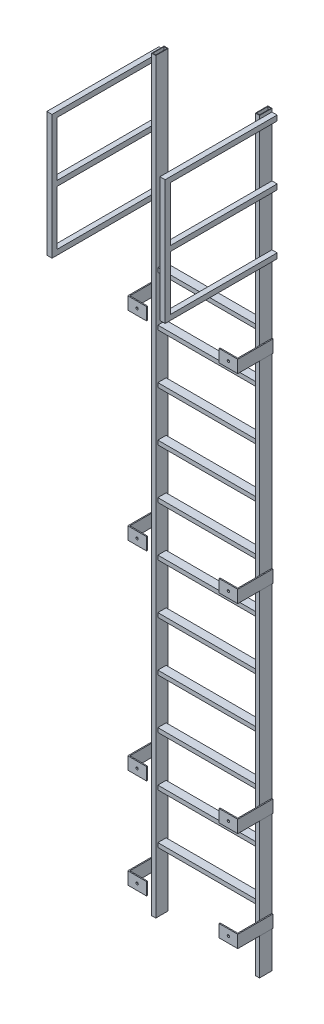
SolidWorks part; units mm, degrees
ref_plane "Front Plane" through (0, 0, 0) normal (0, 0, 1) x (1, 0, 0)
ref_plane "Top Plane" through (0, 0, 0) normal (0, 1, 0) x (1, 0, 0)
ref_plane "Right Plane" through (0, 0, 0) normal (1, 0, 0) x (0, 0, -1)
sketch "Sketch1" plane through (0, 0, 0) normal (0, 0, 1) x (1, 0, 0)
  line L0 (0, 77.2993) -> (0, -101.782) construction
  line L1 (-330.2, 0) -> (-304.8, -4572) construction
  line L2 (330.2, -4572) -> (304.8, -4572)
  line L3 (330.2, -4572) -> (330.2, 0)
  line L4 (330.2, 0) -> (304.8, 0)
  line L5 (304.8, -4572) -> (304.8, 0)
  line L6 (330.2, -4572) -> (304.8, 0) construction
  line L7 (330.2, 0) -> (304.8, -4572) construction
  line L8 (-330.2, -4572) -> (-304.8, 0) construction
  line L9 (-304.8, -4572) -> (-304.8, 0)
  line L10 (-330.2, 0) -> (-304.8, 0)
  line L11 (-330.2, -4572) -> (-330.2, 0)
  line L12 (-330.2, -4572) -> (-304.8, -4572)
  point P3 (317.5, -2286)
  point P12 (-317.5, -2286)
  dimension "D1" = 660.4
  dimension "D2" = 609.6
  dimension "D3" = 25.4
  dimension "D4" = 4572
extrude "Boss-Extrude1" add sketch "Sketch1" along normal mid plane 76.2
sketch "Sketch2" plane through (0, 0, 0) normal (0, 1, 0) x (1, 0, 0)
  line L0 (0, 283.8773) -> (0, -407.33) construction
  line L1 (-561.2677, 0) -> (674.2654, 0) construction
  line L2 (-304.8, 38.1) -> (-330.2, 38.1) construction
  line L3 (-307.975, -34.925) -> (-327.025, -34.925)
  line L4 (-307.975, -34.925) -> (-307.975, 34.925)
  line L5 (-307.975, 34.925) -> (-327.025, 34.925)
  line L6 (-327.025, -34.925) -> (-327.025, 34.925)
  line L7 (-307.975, -34.925) -> (-327.025, 34.925) construction
  line L8 (-307.975, 34.925) -> (-327.025, -34.925) construction
  line L9 (-330.2, -38.1) -> (-330.2, 38.1) construction
  line L10 (-304.8, -38.1) -> (-304.8, 38.1) construction
  line L11 (-304.8, -38.1) -> (-330.2, -38.1) construction
  line L12 (307.975, 34.925) -> (327.025, -34.925) construction
  line L13 (307.975, -34.925) -> (327.025, 34.925) construction
  line L14 (327.025, -34.925) -> (327.025, 34.925)
  line L15 (307.975, 34.925) -> (327.025, 34.925)
  line L16 (307.975, -34.925) -> (307.975, 34.925)
  line L17 (307.975, -34.925) -> (327.025, -34.925)
  point P5 (-317.5, 0)
  point P18 (-317.5, -38.1)
  point P23 (317.5, 0)
  dimension "D1" = 3.175
  dimension "D2" = 3.175
  dimension "D3" = 3.175
  dimension "D4" = 3.175
extrude "Cut-Extrude1" cut sketch "Sketch2" against normal up to next (4572 mm away)
sketch "Sketch3" plane through (304.8, 0, 0) normal (-1, 0, 0) x (0, 0, 1)
  line L0 (0, -4612.9158) -> (0, 785.9283) construction
  line L2 (25.4, -1155.7) -> (-25.4, -1155.7)
  line L3 (25.4, -1155.7) -> (25.4, -1130.3)
  line L4 (25.4, -1130.3) -> (-25.4, -1130.3)
  line L5 (-25.4, -1155.7) -> (-25.4, -1130.3)
  line L6 (25.4, -1155.7) -> (-25.4, -1130.3) construction
  line L7 (25.4, -1130.3) -> (-25.4, -1155.7) construction
  line L8 (19.05, -1149.35) -> (-19.05, -1149.35)
  line L9 (19.05, -1149.35) -> (19.05, -1136.65)
  line L10 (19.05, -1136.65) -> (-19.05, -1136.65)
  line L11 (-19.05, -1149.35) -> (-19.05, -1136.65)
  line L12 (19.05, -1149.35) -> (-19.05, -1136.65) construction
  line L13 (19.05, -1136.65) -> (-19.05, -1149.35) construction
  line L14 (38.1, 0) -> (-38.1, 0) construction
  point P3 (0, -1143)
  point P5 (0, -1143)
  dimension "D1" = 50.8
  dimension "D2" = 25.4
  dimension "D3" = 6.35
  dimension "D4" = 6.35
  dimension "D5" = 1143
extrude "Boss-Extrude2" add sketch "Sketch3" along direction (1, 0, 0) on the side of the normal up to surface (609.6 mm away)
pattern_linear "LPattern1" count 11 spacing 304.8 along (0, -1, 0) of "Boss-Extrude2"
sketch "Sketch4" plane through (0, 0, 0) normal (0, 1, 0) x (1, 0, 0)
  line L0 (330.2, 38.1) -> (336.55, 38.1)
  line L1 (336.55, 38.1) -> (336.55, -177.8)
  line L2 (336.55, -177.8) -> (222.25, -177.8)
  line L3 (222.25, -177.8) -> (222.25, -171.45)
  line L4 (222.25, -171.45) -> (330.2, -171.45)
  line L5 (330.2, -171.45) -> (330.2, 38.1)
  line L6 (0, 284.9189) -> (0, -312.4003) construction
  line L7 (-330.2, -171.45) -> (-330.2, 38.1)
  line L8 (-222.25, -171.45) -> (-330.2, -171.45)
  line L9 (-222.25, -177.8) -> (-222.25, -171.45)
  line L10 (-336.55, -177.8) -> (-222.25, -177.8)
  line L11 (-336.55, 38.1) -> (-336.55, -177.8)
  line L12 (-330.2, 38.1) -> (-336.55, 38.1)
  dimension "D1" = 6.35
  dimension "D2" = 6.35
  dimension "D3" = 215.9
  dimension "D4" = 114.3
extrude "Boss-Extrude3" add sketch "Sketch4" along direction (0, 1, 0) on the side against the normal blind 76.2 from offset 1219.2 offset against normal yes
sketch "Sketch5" plane through (0, 0, 177.8) normal (0, 0, 1) x (1, 0, 0)
  line L0 (0, 893.1398) -> (0, -1460.5357) construction
  circle A0 centre (-279.4, -1257.3) radius 7.1438
  circle A1 centre (279.4, -1257.3) radius 7.1438
  dimension "D1" = 14.2875
extrude "Cut-Extrude2" cut sketch "Sketch5" against normal up to next (6.35 mm away)
pattern_linear "LPattern2" count 3 spacing 1219.2 along (0, -1, 0) of "Boss-Extrude3", "Cut-Extrude2"
pattern_linear "LPattern3" count 2 spacing 3048 along (0, -1, 0) of "Boss-Extrude3", "Cut-Extrude2"
sketch "Sketch8" plane through (0, 0, -38.1) normal (0, 0, -1) x (-1, 0, 0)
  line L0 (0, 1695.4544) -> (0, -6125.6815) construction
  line L1 (-330.2, -1219.2) -> (-330.2, 0) construction
  line L2 (-330.2, -19.7351) -> (-361.95, -19.7351)
  line L3 (-330.2, -19.7351) -> (-330.2, -51.4851)
  line L4 (-330.2, -51.4851) -> (-361.95, -51.4851)
  line L5 (-361.95, -19.7351) -> (-361.95, -51.4851)
  line L6 (-361.95, -384.9871) -> (-361.95, -416.7371)
  line L7 (-330.2, -384.9871) -> (-330.2, -416.7371)
  line L8 (-330.2, -384.9871) -> (-361.95, -384.9871)
  line L9 (-330.2, -416.7371) -> (-361.95, -416.7371)
  line L10 (-361.95, -750.2391) -> (-361.95, -781.9891)
  line L11 (-330.2, -750.2391) -> (-330.2, -781.9891)
  line L12 (-330.2, -750.2391) -> (-361.95, -750.2391)
  line L13 (-330.2, -781.9891) -> (-361.95, -781.9891)
  line L14 (330.2, -781.9891) -> (361.95, -781.9891)
  line L15 (330.2, -750.2391) -> (361.95, -750.2391)
  line L16 (330.2, -750.2391) -> (330.2, -781.9891)
  line L17 (361.95, -750.2391) -> (361.95, -781.9891)
  line L18 (330.2, -416.7371) -> (361.95, -416.7371)
  line L19 (330.2, -384.9871) -> (361.95, -384.9871)
  line L20 (330.2, -384.9871) -> (330.2, -416.7371)
  line L21 (361.95, -384.9871) -> (361.95, -416.7371)
  line L22 (361.95, -19.7351) -> (361.95, -51.4851)
  line L23 (330.2, -51.4851) -> (361.95, -51.4851)
  line L24 (330.2, -19.7351) -> (330.2, -51.4851)
  line L25 (330.2, -19.7351) -> (361.95, -19.7351)
  dimension "D1" = 31.75
  dimension "D2" = 31.75
  dimension "D3" = 3
extrude "Boss-Extrude4" add sketch "Sketch8" against normal blind 685.8
sketch "Sketch9" plane through (0, 0, 647.7) normal (0, 0, 1) x (1, 0, 0)
  line L0 (0, 455.8149) -> (0, -1114.3214) construction
  line L2 (-361.95, -19.7351) -> (-330.2, -19.7351)
  line L3 (-361.95, -19.7351) -> (-361.95, -781.9891)
  line L4 (-361.95, -781.9891) -> (-330.2, -781.9891)
  line L5 (-330.2, -19.7351) -> (-330.2, -781.9891)
  line L6 (330.2, -19.7351) -> (361.95, -19.7351)
  line L7 (330.2, -19.7351) -> (330.2, -781.9891)
  line L8 (330.2, -781.9891) -> (361.95, -781.9891)
  line L9 (361.95, -19.7351) -> (361.95, -781.9891)
extrude "Boss-Extrude5" add sketch "Sketch9" against normal blind 31.75
